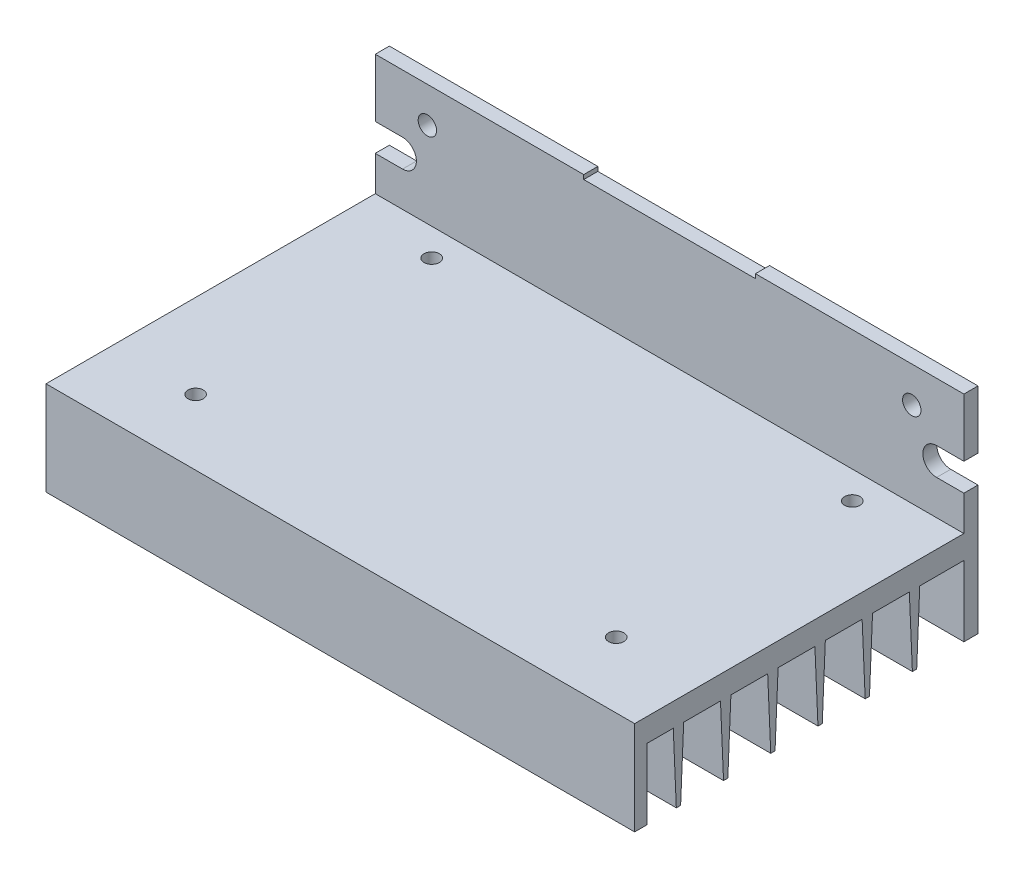
SolidWorks part; units mm, degrees
material "356.0-T6 Permanent Mold cast (SS)"
ref_plane "Front Plane" through (0, 0, 0) normal (0, 0, 1) x (1, 0, 0)
ref_plane "Top Plane" through (0, 0, 0) normal (0, 1, 0) x (1, 0, 0)
ref_plane "Right Plane" through (0, 0, 0) normal (1, 0, 0) x (0, 0, -1)
sketch "Sketch1" plane through (0, 0, 0) normal (0, 1, 0) x (1, 0, 0)
  line L1 (-48, 28) -> (48, 28)
  line L2 (-48, 28) -> (-48, -28)
  line L3 (-48, -28) -> (48, -28)
  line L4 (48, 28) -> (48, -28)
  line L5 (-48, 28) -> (48, -28) construction
  line L6 (-48, -28) -> (48, 28) construction
  point P0 (0, 0)
  dimension "D1" = 96
  dimension "D2" = 56
extrude "Boss-Extrude1" add sketch "Sketch1" along normal blind 3.8
sketch "Sketch2" plane through (0, 0, -28) normal (0, 0, -1) x (-1, 0, 0)
  line L0 (-48, 3.8) -> (-48, 0) construction
  line L1 (-48, 23.5) -> (48, 23.5)
  line L2 (-48, 23.5) -> (-48, -11.5)
  line L3 (-48, -11.5) -> (48, -11.5)
  line L4 (48, 23.5) -> (48, -11.5)
  line L5 (48, 3.8) -> (48, 0) construction
  line L7 (-48, 0) -> (48, 0) construction
  dimension "D1" = 35
  dimension "D2" = 11.5
extrude "Boss-Extrude2" add sketch "Sketch2" against normal blind 2.3
sketch "Sketch3" plane through (0, 0, -25.7) normal (0, 0, -1) x (-1, 0, 0)
  line L0 (-52.45, 11.75) -> (-43.55, 11.75) construction
  line L1 (-48, 23.5) -> (-48, -11.5) construction
  line L2 (-52.45, 14) -> (-43.55, 14)
  line L3 (-52.45, 9.5) -> (-43.55, 9.5)
  line L4 (-43.55, 11.75) -> (-41.3, 11.75) construction
  line L5 (-48, -11.5) -> (48, -11.5) construction
  line L6 (48, 23.5) -> (-48, 23.5) construction
  arc A0 (-52.45, 14) -> (-52.45, 9.5) centre (-52.45, 11.75) ccw
  arc A1 (-43.55, 9.5) -> (-43.55, 14) centre (-43.55, 11.75) ccw
  point P4 (-48, 11.75)
  dimension "D2" = 4.5
  dimension "D1" = 6.7
  dimension "D3" = 9.5
  dimension "D4" = 23.25
extrude "Cut-Extrude1" cut sketch "Sketch3" along normal through all
sketch "Sketch4" plane through (0, 0, -25.7) normal (0, 0, 1) x (1, 0, 0)
  line L1 (48, 9.5) -> (48, 3.8) construction
  line L2 (-48, 23.5) -> (48, 23.5) construction
  circle A0 centre (39.5, 17.7) radius 1.5
  dimension "D3" = 3
  dimension "D1" = 5.8
  dimension "D2" = 8.5
extrude "Cut-Extrude2" cut sketch "Sketch4" against normal through all
mirror "Mirror1" about plane through (0, 0, 0) normal (1, 0, 0) of "Cut-Extrude2", "Cut-Extrude1"
sketch "Sketch5" plane through (0, 0, 0) normal (0, 1, 0) x (1, 0, 0)
  line L0 (48, -28) -> (48, 25.7) construction
  line L1 (-48, -28) -> (48, -28)
  line L2 (-48, -28) -> (-48, -26)
  line L3 (-48, -26) -> (48, -26)
  line L4 (48, -28) -> (48, -26)
  dimension "D1" = 2
extrude "Boss-Extrude3" add sketch "Sketch5" against normal up to surface (11.5 mm away) up to face at (0, -11.5, -26.85)
sketch "Sketch7" plane through (0, 0, 0) normal (1, 0, 0) x (0, 0, -1)
  line L0 (-21.7, 0) -> (-21.2, -11.5)
  line L1 (-21.2, -11.5) -> (-20.5, -11.5)
  line L2 (-20.5, -11.5) -> (-20, 0)
  line L3 (-20, 0) -> (-21.7, 0)
  line L4 (-26, 0) -> (25.7, 0) construction
  line L5 (25.7, -11.5) -> (28, -11.5) construction
  line L7 (-20.85, 0) -> (-20.85, -11.5) construction
  line L8 (-26, -11.5) -> (-26, 0) construction
  dimension "D1" = 1.7
  dimension "D2" = 0.7
  dimension "D3" = 4.3
extrude "Boss-Extrude5" add sketch "Sketch7" along normal up to surface (48 mm away) and the other way up to surface (48 mm away) up to face at (48, 18.75, -26.85) other way up to face at (-48, 18.75, -26.85)
pattern_linear "LPattern1" count 6 spacing 7.7 along (0, 0, -1) of "Boss-Extrude5"
sketch "Sketch8" plane through (0, 23.5, 0) normal (0, 1, 0) x (1, 0, 0)
  line L0 (-48, 28) -> (48, 28) construction
  line L1 (-14, 28) -> (14, 28)
  line L2 (-14, 28) -> (-14, 25.7)
  line L3 (-14, 25.7) -> (14, 25.7)
  line L4 (14, 28) -> (14, 25.7)
  line L5 (-48, 25.7) -> (48, 25.7) construction
  point P8 (0, 28)
  dimension "D1" = 28
extrude "Cut-Extrude3" cut sketch "Sketch8" against normal blind 0.7
hole_wizard "M3x0.5 Tapped Hole1" positions "Sketch9" profile "Sketch10" tap size "M3x0.5" standard "ANSI Metric" end condition through all
sketch "Sketch9" plane through (0, 3.8, 0) normal (0, 1, 0) x (1, 0, 0)
  line L7 (34.3, -17.3) -> (-34.3, -17.3) construction
  line L9 (0, 0) -> (0, -17.3) construction
  line L11 (-48, -28) -> (48, -28) construction
  point P0 (-34.3, -17.3)
  point P3 (34.3, -17.3)
  dimension "D2" = 68.6
  dimension "D3" = 10.7
sketch "Sketch10" plane through (-34.3, 3.8, 17.3) normal (1, 0, 0) x (0, 0, 1)
  line L0 (0, 0) -> (0, 15.3)
  line L1 (0, 15.3) -> (1.25, 15.3)
  line L2 (1.25, 15.3) -> (1.25, 0)
  line L5 (1.25, 0) -> (0, 0)
  line L11 (0, -6.35) -> (0, 107.95) construction
  dimension "Thru Tap Drill Dia." = 2.5
  dimension "Thru Tap Drill Depth" = 15.3
cosmetic thread "Hole Thread2" parameters "D2"=3
cosmetic thread "Hole Thread3" parameters "D2"=3
pattern_linear "LPattern2" count 2 spacing 38.5 along (0, 0, -1) of "M3x0.5 Tapped Hole1"
